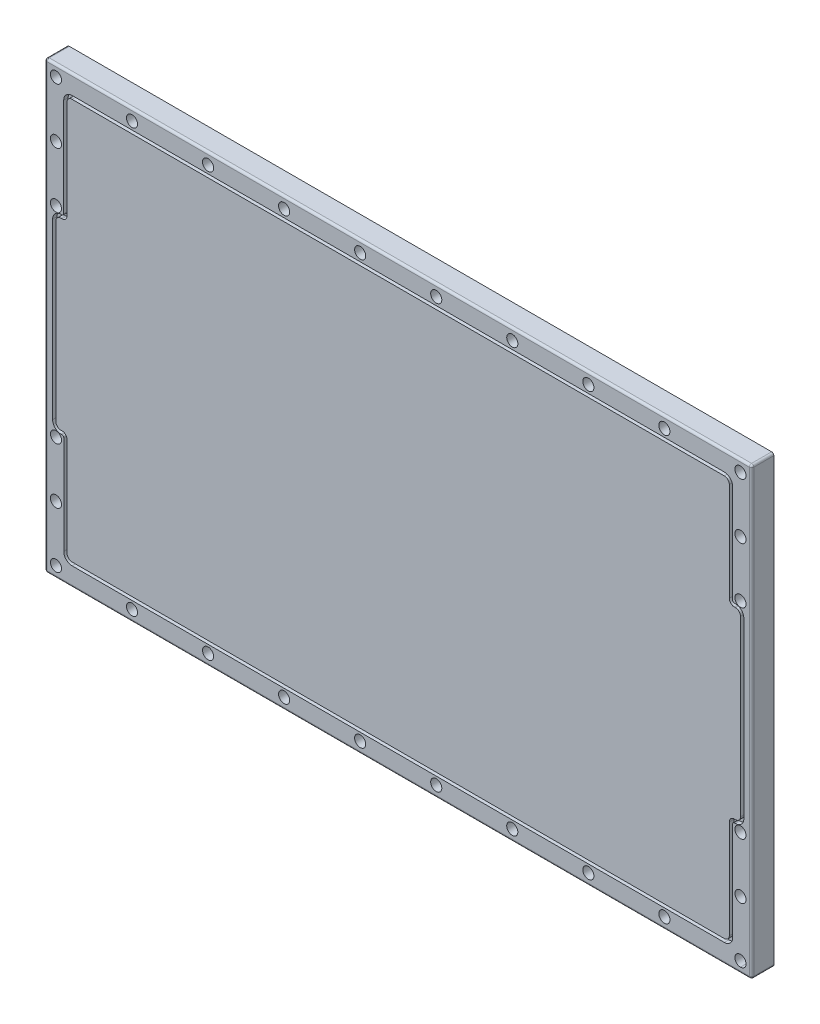
SolidWorks part; units mm, degrees
ref_plane "Front Plane" through (0, 0, 0) normal (0, 0, 1) x (1, 0, 0)
ref_plane "Top Plane" through (0, 0, 0) normal (0, 1, 0) x (1, 0, 0)
ref_plane "Right Plane" through (0, 0, 0) normal (1, 0, 0) x (0, 0, -1)
sketch "Sketch2" plane through (0, 0, 0) normal (0, 0, 1) x (1, 0, 0)
  line L1 (0, 0) -> (635, 0)
  line L2 (0, 0) -> (0, 400)
  line L3 (0, 400) -> (635, 400)
  line L4 (635, 0) -> (635, 400)
  dimension "D1" = 635
  dimension "D2" = 400
extrude "Boss-Extrude1" add sketch "Sketch2" along normal mid plane 20
sketch "Sketch4" plane through (0, 0, 10) normal (0, 0, 1) x (1, 0, 0)
  circle A0 centre (10, 10) radius 5
  dimension "D1" = 10
  dimension "D2" = 10
  dimension "D3" = 10
extrude "Cut-Extrude1" cut sketch "Sketch4" against normal blind 20
pattern_linear "LPattern1" count 10 spacing 68.33 along (1, 0, 0) count 2 spacing 380 along (0, 1, 0) of "Cut-Extrude1"
pattern_linear "LPattern3" count 3 spacing 50 along (0, 1, 0) count 2 spacing 615 along (1, 0, 0) of "Cut-Extrude1"
pattern_linear "LPattern4" count 2 spacing 330 along (0, 1, 0) of "Cut-Extrude1"
sketch "Sketch7" plane through (0, 0, 10) normal (0, 0, 1) x (1, 0, 0)
  line L0 (635, 0) -> (635, 400) construction
  circle A0 centre (625, 340) radius 5
  point P6 (635, 375.9728)
  point P7 (626.0795, 333.9109)
  point P8 (635, 394.1171)
  dimension "D1" = 10
  dimension "D2" = 10
  dimension "D3" = 60
extrude "Cut-Extrude5" cut sketch "Sketch7" against normal blind 20
pattern_linear "LPattern7" count 2 spacing 615 along (-1, 0, 0) count 2 spacing 50 along (0, -1, 0) of "Cut-Extrude5"
sketch "Sketch8" plane through (0, 0, 10) normal (0, 0, 1) x (1, 0, 0)
  line L0 (20, 113) -> (20, 24.5)
  line L1 (24.5, 20) -> (610.5, 20)
  line L6 (614.97, 287) -> (614.97, 375.5)
  line L7 (610.47, 380) -> (24.47, 380)
  line L8 (19.97, 375.5) -> (19.97, 287)
  line L13 (0, 0) -> (635, 0) construction
  line L14 (0, 400) -> (0, 0) construction
  line L15 (15.47, 282.5) -> (14.47, 282.5)
  line L16 (9.97, 278) -> (9.97, 122)
  line L17 (14.47, 117.5) -> (15.5, 117.5)
  line L21 (615, 24.5) -> (615, 113)
  line L22 (619.5, 117.5) -> (620.5, 117.5)
  line L23 (625, 122) -> (625, 278)
  line L24 (620.5, 282.5) -> (619.47, 282.5)
  line L26 (16.97, 375.5) -> (16.97, 287)
  line L27 (15.47, 285.5) -> (14.47, 285.5)
  line L28 (6.97, 278) -> (6.97, 122)
  line L29 (14.47, 114.5) -> (15.5, 114.5)
  line L30 (17, 113) -> (17, 24.5)
  line L31 (24.5, 17) -> (610.5, 17)
  line L32 (618, 24.5) -> (618, 113)
  line L33 (619.5, 114.5) -> (620.5, 114.5)
  line L34 (628, 122) -> (628, 278)
  line L35 (620.5, 285.5) -> (619.47, 285.5)
  line L36 (617.97, 287) -> (617.97, 375.5)
  line L37 (610.47, 383) -> (24.47, 383)
  circle A1 centre (624.97, 390) radius 5 construction
  arc A4 (19.97, 375.5) -> (24.47, 380) centre (24.47, 375.5) cw
  arc A5 (15.47, 282.5) -> (19.97, 287) centre (15.47, 287) ccw
  arc A6 (9.97, 278) -> (14.47, 282.5) centre (14.47, 278) cw
  arc A7 (14.47, 117.5) -> (9.97, 122) centre (14.47, 122) cw
  arc A8 (20, 113) -> (15.5, 117.5) centre (15.5, 113) ccw
  arc A9 (20, 24.5) -> (24.5, 20) centre (24.5, 24.5) ccw
  arc A10 (610.5, 20) -> (615, 24.5) centre (610.5, 24.5) ccw
  arc A11 (619.5, 117.5) -> (615, 113) centre (619.5, 113) ccw
  arc A12 (620.5, 117.5) -> (625, 122) centre (620.5, 122) ccw
  arc A13 (625, 278) -> (620.5, 282.5) centre (620.5, 278) ccw
  arc A14 (619.47, 282.5) -> (614.97, 287) centre (619.47, 287) cw
  arc A15 (614.97, 375.5) -> (610.47, 380) centre (610.47, 375.5) ccw
  arc A16 (15.47, 285.5) -> (16.97, 287) centre (15.47, 287) ccw
  arc A17 (6.97, 278) -> (14.47, 285.5) centre (14.47, 278) cw
  arc A18 (14.47, 114.5) -> (6.97, 122) centre (14.47, 122) cw
  arc A19 (17, 113) -> (15.5, 114.5) centre (15.5, 113) ccw
  arc A20 (17, 24.5) -> (24.5, 17) centre (24.5, 24.5) ccw
  arc A21 (610.5, 17) -> (618, 24.5) centre (610.5, 24.5) ccw
  arc A22 (619.5, 114.5) -> (618, 113) centre (619.5, 113) ccw
  arc A23 (620.5, 114.5) -> (628, 122) centre (620.5, 122) ccw
  arc A24 (628, 278) -> (620.5, 285.5) centre (620.5, 278) ccw
  arc A25 (619.47, 285.5) -> (617.97, 287) centre (619.47, 287) cw
  arc A26 (617.97, 375.5) -> (610.47, 383) centre (610.47, 375.5) ccw
  arc A27 (16.97, 375.5) -> (24.47, 383) centre (24.47, 375.5) cw
  point P22 (19.97, 380)
  point P23 (19.97, 282.5)
  point P26 (9.97, 282.5)
  point P29 (9.97, 117.5)
  point P32 (20, 117.5)
  point P35 (20, 20)
  point P38 (615, 20)
  point P41 (615, 117.5)
  point P44 (625, 117.5)
  point P47 (625, 282.5)
  point P52 (614.97, 380)
  dimension "D14" = 4.5
  dimension "D1" = 595
  dimension "D2" = 97.5
  dimension "D3" = 10
  dimension "D4" = 20
  dimension "D5" = 20
  dimension "D6" = 10
  dimension "D7" = 97.5
  dimension "D8" = 595
  dimension "D9" = 165
  dimension "D10" = 165
  dimension "D11" = 20
  dimension "D12" = 97.5
  dimension "D13" = 10
  dimension "D15" = 3
extrude "Cut-Extrude6" cut sketch "Sketch8" against normal blind 4
fillet "Fillet1" radius 2 8 edges at (0, 0, 0) (635, 0, 0) (317.5, 0, 10) (0, 200, 10) (0, 400, 0) (635, 200, 10) (317.5, 400, 10) (635, 400, 0)
